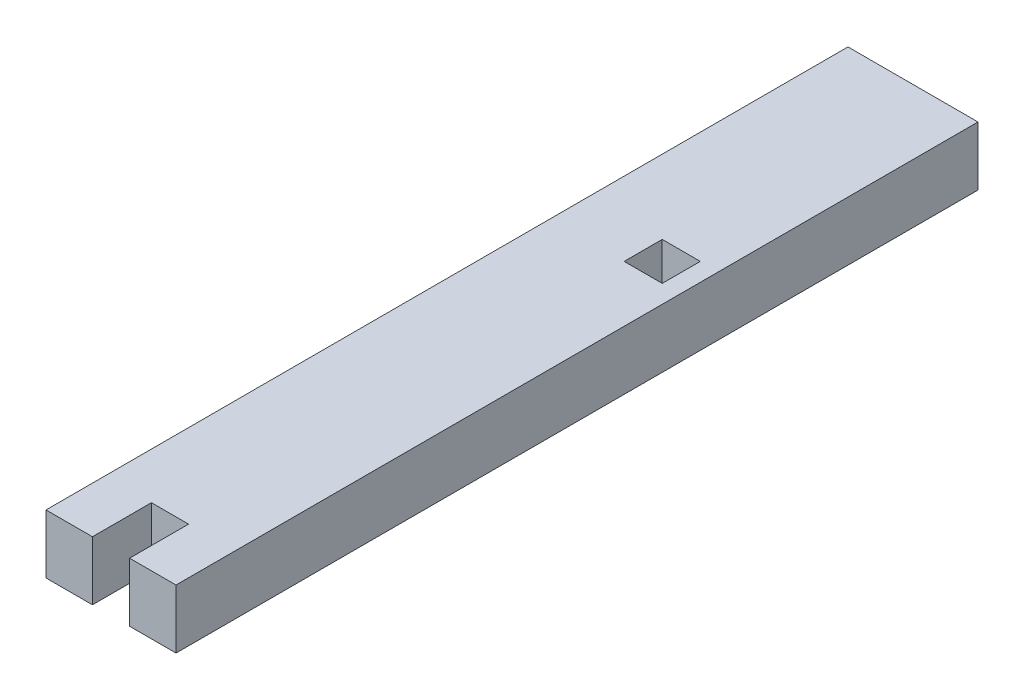
SolidWorks part; units mm, degrees
material "Acrylic (Medium-high impact)"
ref_plane "Front Plane" through (0, 0, 0) normal (0, 0, 1) x (1, 0, 0)
ref_plane "Top Plane" through (0, 0, 0) normal (0, 1, 0) x (1, 0, 0)
ref_plane "Right Plane" through (0, 0, 0) normal (1, 0, 0) x (0, 0, -1)
sketch "Sketch1" plane through (0, 0, 0) normal (0, 1, 0) x (1, 0, 0)
  line L1 (3.5, -21.5875) -> (-3.5, -21.5875)
  line L2 (3.5, -21.5875) -> (3.5, 21.5875)
  line L3 (3.5, 21.5875) -> (-3.5, 21.5875)
  line L4 (-3.5, -21.5875) -> (-3.5, 21.5875)
  line L5 (3.5, -21.5875) -> (-3.5, 21.5875) construction
  line L6 (3.5, 21.5875) -> (-3.5, -21.5875) construction
  line L7 (0.475, 7.6125) -> (2.525, 7.6125)
  line L8 (0.475, 7.6125) -> (0.475, 5.5625)
  line L9 (0.475, 5.5625) -> (2.525, 5.5625)
  line L10 (2.525, 7.6125) -> (2.525, 5.5625)
  line L11 (0.475, 7.6125) -> (2.525, 5.5625) construction
  line L12 (0.475, 5.5625) -> (2.525, 7.6125) construction
  line L13 (-1, -21.5875) -> (1, -21.5875)
  line L14 (-1, -21.5875) -> (-1, -18.4125)
  line L15 (-1, -18.4125) -> (1, -18.4125)
  line L16 (1, -21.5875) -> (1, -18.4125)
  line L21 (-3.5, -21.5875) -> (-6.675, -21.5875)
  line L22 (-3.5, -21.5875) -> (-3.5, -14.5875)
  line L23 (-3.5, -14.5875) -> (-6.675, -14.5875)
  line L24 (-6.675, -21.5875) -> (-6.675, -14.5875)
  line L25 (-6.675, -17.0875) -> (-3.5, -17.0875)
  line L26 (-6.675, -17.0875) -> (-6.675, -19.0875)
  line L27 (-6.675, -19.0875) -> (-3.5, -19.0875)
  line L28 (-3.5, -17.0875) -> (-3.5, -19.0875)
  point P0 (0, 0)
  point P6 (1.5, 6.5875)
  point P11 (0, -18.4125)
  point P24 (-6.675, -18.0875)
  point P25 (-6.675, -18.0875)
  dimension "D1" = 7
  dimension "D3" = 2.05
  dimension "D6" = 2
  dimension "D7" = 3.175
  dimension "D5" = 5
  dimension "D4" = 15
  dimension "D8" = 7
  dimension "D9" = 3.175
  dimension "D10" = 2
  dimension "D2" = 40
extrude "Boss-Extrude1" add sketch "Sketch1" along normal blind 3.175 contours L16 L1 L2 L3 L4 L14 L15 L7 L10 L9 L8
equation "\"bottomThickness\"= .25in"
equation "\"wallThickness\"= .125in"
equation "\"D1@Boss-Extrude1\"=\"wallThickness\""
equation "\"D9@Sketch1\"=\"wallThickness\""
equation "\"D7@Sketch1\"=\"wallThickness\""
